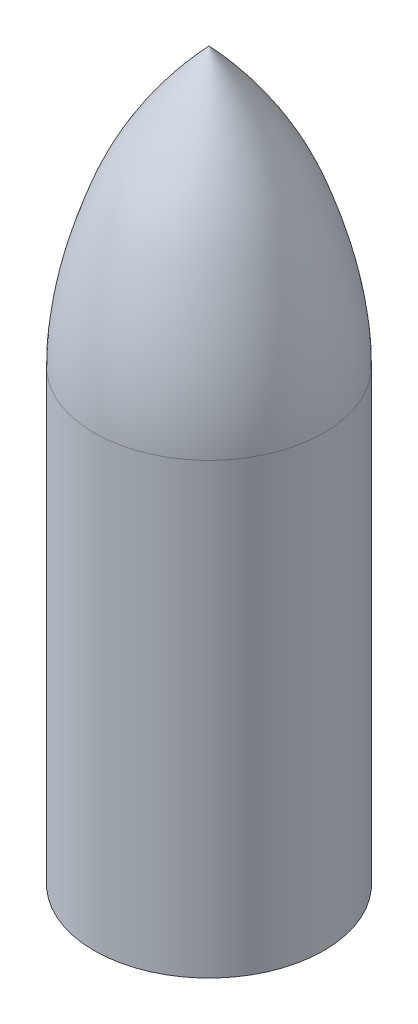
SolidWorks part; units mm, degrees
ref_plane "Front Plane" through (0, 0, 0) normal (0, 0, 1) x (1, 0, 0)
ref_plane "Top Plane" through (0, 0, 0) normal (0, 1, 0) x (1, 0, 0)
ref_plane "Right Plane" through (0, 0, 0) normal (1, 0, 0) x (0, 0, -1)
sketch "Sketch1" plane through (0, 0, 0) normal (0, 1, 0) x (1, 0, 0)
  line L1 (-39.9611, 9.1711) -> (39.9611, 9.1711)
  line L2 (-39.9611, -9.1711) -> (39.9611, -9.1711)
  line L3 (-36.974, 9.1711) -> (-36.974, -17.7179)
  line L4 (37.026, 9.1711) -> (37.026, -9.1711)
  line L5 (-41, 0) -> (41, 0)
  circle A0 centre (0, 0) radius 41
  circle A1 centre (0, 0) radius 25
  circle A2 centre (0, 0) radius 26
  circle A3 centre (0, 0) radius 27
  dimension "D1" = 82
  dimension "D2" = 50
  dimension "D5" = 52
  dimension "D6" = 37.026
  dimension "D3" = 74
  dimension "D4" = 53
  dimension "D7" = 39.9611
extrude "Boss-Extrude1" add sketch "Sketch1" against normal blind 160 contours L5 A0 L1 L4 | L2 A0 L5 L4 | L5 A0 L2 L3 | A3 L2 L3 A0 | L1 A0 L5 L3 | A3 L1 A0 | L2 A0 L3
sketch "Sketch2" plane through (0, 0, 0) normal (0, 0, 1) x (1, 0, 0)
  line L0 (0, 0) -> (0, 73.8378) construction
  line L1 (0, 0) -> (0, 99.0646)
  line L2 (41, 0) -> (0, 0)
  spline S0 degree 3 poles (0, 99.0646) (11.4357, 87.036) (23.6472, 70.3282) (36.3881, 36.3296) (40.9692, 16.5594) (41, 0) knots 0 0 0 0 0.458505 0.547538 1 1 1 1
revolve "Revolve1" add sketch "Sketch2" angle 360 about L1
